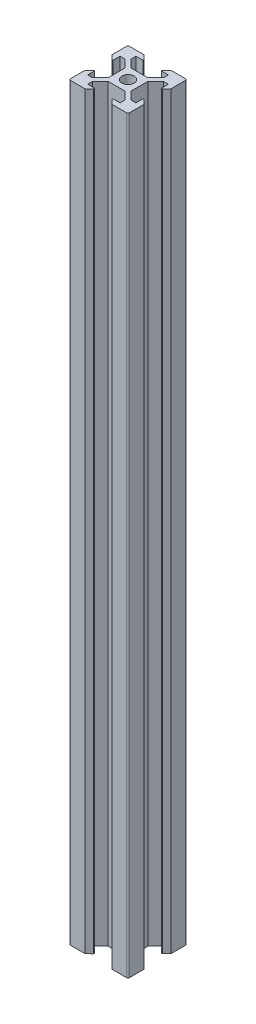
SolidWorks part; units mm, degrees
ref_plane "Front Plane" through (0, 0, 0) normal (0, 0, 1) x (1, 0, 0)
ref_plane "Top Plane" through (0, 0, 0) normal (0, 1, 0) x (1, 0, 0)
ref_plane "Right Plane" through (0, 0, 0) normal (1, 0, 0) x (0, 0, -1)
sketch "Sketch1" plane through (0, 0, 0) normal (1, 0, 0) x (0, 0, -1)
  line L0 (0, 0) -> (0, 254)
  dimension "D1" = 254
other "Vslot2020 2020(5)"
ref_plane "Plane5" through (0, 0, 0) normal (0, 1, 0) x (0, 0, 1)
sketch "Sketch2" plane through (0, 0, 0) normal (0, 1, 0) x (0, 0, 1)
  line L58 (13.9, 7.1491) -> (13.9, 12.8445)
  line L59 (13.9, 12.8445) -> (16.5585, 15.4922)
  line L60 (16.5585, 15.4922) -> (16.5507, 15.5)
  line L61 (16.5507, 15.5) -> (18.2, 15.5)
  line L62 (18.2, 15.5) -> (18.2, 13.12)
  line L63 (18.2, 13.12) -> (18.5344, 13.12)
  line L64 (18.5344, 13.12) -> (20, 14.58)
  line L65 (20, 14.58) -> (20, 19.5)
  line L66 (19.5, 20) -> (14.575, 20)
  line L67 (14.575, 20) -> (13.12, 18.545)
  line L68 (13.12, 18.545) -> (13.12, 18.2)
  line L69 (13.12, 18.2) -> (15.5, 18.2)
  line L70 (15.5, 18.2) -> (15.5, 16.555)
  line L71 (15.5, 16.555) -> (12.8341, 13.9)
  line L72 (12.8341, 13.9) -> (7.155, 13.9)
  line L73 (7.155, 13.9) -> (4.5, 16.555)
  line L74 (4.5, 16.555) -> (4.5, 18.2)
  line L75 (4.5, 18.2) -> (6.875, 18.2)
  line L76 (6.875, 18.2) -> (6.875, 18.545)
  line L77 (6.875, 18.545) -> (5.42, 20)
  line L78 (5.42, 20) -> (0.5, 20)
  line L79 (0, 19.5) -> (0, 14.58)
  line L80 (0, 14.58) -> (1.46, 13.12)
  line L81 (1.46, 13.12) -> (1.8, 13.12)
  line L82 (1.8, 13.12) -> (1.8, 15.5)
  line L83 (1.8, 15.5) -> (3.445, 15.5)
  line L84 (3.445, 15.5) -> (3.4393, 15.4943)
  line L85 (3.4393, 15.4943) -> (6.0943, 12.8393)
  line L86 (6.0943, 12.8393) -> (6.1, 12.845)
  line L87 (6.1, 12.845) -> (6.1, 7.1491)
  line L88 (6.1, 7.1491) -> (3.4393, 4.5)
  line L89 (3.4393, 4.5) -> (1.8, 4.5)
  line L90 (1.8, 4.5) -> (1.8, 6.88)
  line L91 (1.8, 6.88) -> (1.46, 6.88)
  line L92 (1.46, 6.88) -> (0, 5.42)
  line L93 (0, 5.42) -> (0, 0.5)
  line L94 (0.5, 0) -> (5.42, 0)
  line L95 (5.42, 0) -> (6.875, 1.455)
  line L96 (6.875, 1.455) -> (6.875, 1.8)
  line L97 (6.875, 1.8) -> (4.5, 1.8)
  line L98 (4.5, 1.8) -> (4.5, 3.4393)
  line L99 (4.5, 3.4393) -> (7.1583, 6.0861)
  line L100 (7.1583, 6.0861) -> (7.1445, 6.1)
  line L101 (7.1445, 6.1) -> (12.8546, 6.1)
  line L102 (12.8546, 6.1) -> (12.8412, 6.0865)
  line L103 (12.8412, 6.0865) -> (15.4997, 3.4375)
  line L104 (15.4997, 3.4375) -> (15.5, 3.4377)
  line L105 (15.5, 3.4377) -> (15.5, 1.8)
  line L106 (15.5, 1.8) -> (13.12, 1.8)
  line L107 (13.12, 1.8) -> (13.12, 1.455)
  line L108 (13.12, 1.455) -> (14.575, 0)
  line L109 (14.575, 0) -> (19.5, 0)
  line L110 (20, 0.5) -> (20, 5.42)
  line L111 (20, 5.42) -> (18.6069, 6.88)
  line L112 (18.6069, 6.88) -> (18.2, 6.88)
  line L113 (18.2, 6.88) -> (18.2, 4.5)
  line L114 (18.2, 4.5) -> (16.5585, 4.5)
  line L115 (16.5585, 4.5) -> (13.9, 7.1491)
  line L116 (13.9, 7.1491) -> (13.9, 12.8445)
  line L117 (13.9, 12.8445) -> (16.5585, 15.4922)
  line L118 (16.5585, 15.4922) -> (16.5507, 15.5)
  line L119 (16.5507, 15.5) -> (18.2, 15.5)
  line L120 (18.2, 15.5) -> (18.2, 13.12)
  line L121 (18.2, 13.12) -> (18.5344, 13.12)
  line L122 (18.5344, 13.12) -> (20, 14.58)
  line L123 (20, 14.58) -> (20, 19.5)
  line L124 (19.5, 20) -> (14.575, 20)
  line L125 (14.575, 20) -> (13.12, 18.545)
  line L126 (13.12, 18.545) -> (13.12, 18.2)
  line L127 (13.12, 18.2) -> (15.5, 18.2)
  line L128 (15.5, 18.2) -> (15.5, 16.555)
  line L129 (15.5, 16.555) -> (12.8341, 13.9)
  line L130 (12.8341, 13.9) -> (7.155, 13.9)
  line L131 (7.155, 13.9) -> (4.5, 16.555)
  line L132 (4.5, 16.555) -> (4.5, 18.2)
  line L133 (4.5, 18.2) -> (6.875, 18.2)
  line L134 (6.875, 18.2) -> (6.875, 18.545)
  line L135 (6.875, 18.545) -> (5.42, 20)
  line L136 (5.42, 20) -> (0.5, 20)
  line L137 (0, 19.5) -> (0, 14.58)
  line L138 (0, 14.58) -> (1.46, 13.12)
  line L139 (1.46, 13.12) -> (1.8, 13.12)
  line L140 (1.8, 13.12) -> (1.8, 15.5)
  line L141 (1.8, 15.5) -> (3.445, 15.5)
  line L142 (3.445, 15.5) -> (3.4393, 15.4943)
  line L143 (3.4393, 15.4943) -> (6.0943, 12.8393)
  line L144 (6.0943, 12.8393) -> (6.1, 12.845)
  line L145 (6.1, 12.845) -> (6.1, 7.1491)
  line L146 (6.1, 7.1491) -> (3.4393, 4.5)
  line L147 (3.4393, 4.5) -> (1.8, 4.5)
  line L148 (1.8, 4.5) -> (1.8, 6.88)
  line L149 (1.8, 6.88) -> (1.46, 6.88)
  line L150 (1.46, 6.88) -> (0, 5.42)
  line L151 (0, 5.42) -> (0, 0.5)
  line L152 (0.5, 0) -> (5.42, 0)
  line L153 (5.42, 0) -> (6.875, 1.455)
  line L154 (6.875, 1.455) -> (6.875, 1.8)
  line L155 (6.875, 1.8) -> (4.5, 1.8)
  line L156 (4.5, 1.8) -> (4.5, 3.4393)
  line L157 (4.5, 3.4393) -> (7.1583, 6.0861)
  line L158 (7.1583, 6.0861) -> (7.1445, 6.1)
  line L159 (7.1445, 6.1) -> (12.8546, 6.1)
  line L160 (12.8546, 6.1) -> (12.8412, 6.0865)
  line L161 (12.8412, 6.0865) -> (15.4997, 3.4375)
  line L162 (15.4997, 3.4375) -> (15.5, 3.4377)
  line L163 (15.5, 3.4377) -> (15.5, 1.8)
  line L164 (15.5, 1.8) -> (13.12, 1.8)
  line L165 (13.12, 1.8) -> (13.12, 1.455)
  line L166 (13.12, 1.455) -> (14.575, 0)
  line L167 (14.575, 0) -> (19.5, 0)
  line L168 (20, 0.5) -> (20, 5.42)
  line L169 (20, 5.42) -> (18.6069, 6.88)
  line L170 (18.6069, 6.88) -> (18.2, 6.88)
  line L171 (18.2, 6.88) -> (18.2, 4.5)
  line L172 (18.2, 4.5) -> (16.5585, 4.5)
  line L173 (16.5585, 4.5) -> (13.9, 7.1491)
  circle A0 centre (10, 10) radius 2.0746 construction
  circle A1 centre (10, 10) radius 2.0746
  arc A4 (20, 19.5) -> (19.5, 20) centre (19.5, 19.5) ccw
  arc A5 (0.5, 20) -> (0, 19.5) centre (0.5, 19.5) ccw
  arc A6 (0, 0.5) -> (0.5, 0) centre (0.5, 0.5) ccw
  arc A7 (19.5, 0) -> (20, 0.5) centre (19.5, 0.5) ccw
  arc A8 (20, 19.5) -> (19.5, 20) centre (19.5, 19.5) ccw
  arc A9 (0.5, 20) -> (0, 19.5) centre (0.5, 19.5) ccw
  arc A10 (0, 0.5) -> (0.5, 0) centre (0.5, 0.5) ccw
  arc A11 (19.5, 0) -> (20, 0.5) centre (19.5, 0.5) ccw
  point P16 (0, 0)
  dimension "D1" = 0
ref_plane "Plane6" through (0, 0, 9.9946) normal (0, 0, 1) x (1, 0, 0)
ref_plane "Plane7" through (9.997, 0, 0) normal (1, 0, 0) x (0, 0, -1)
